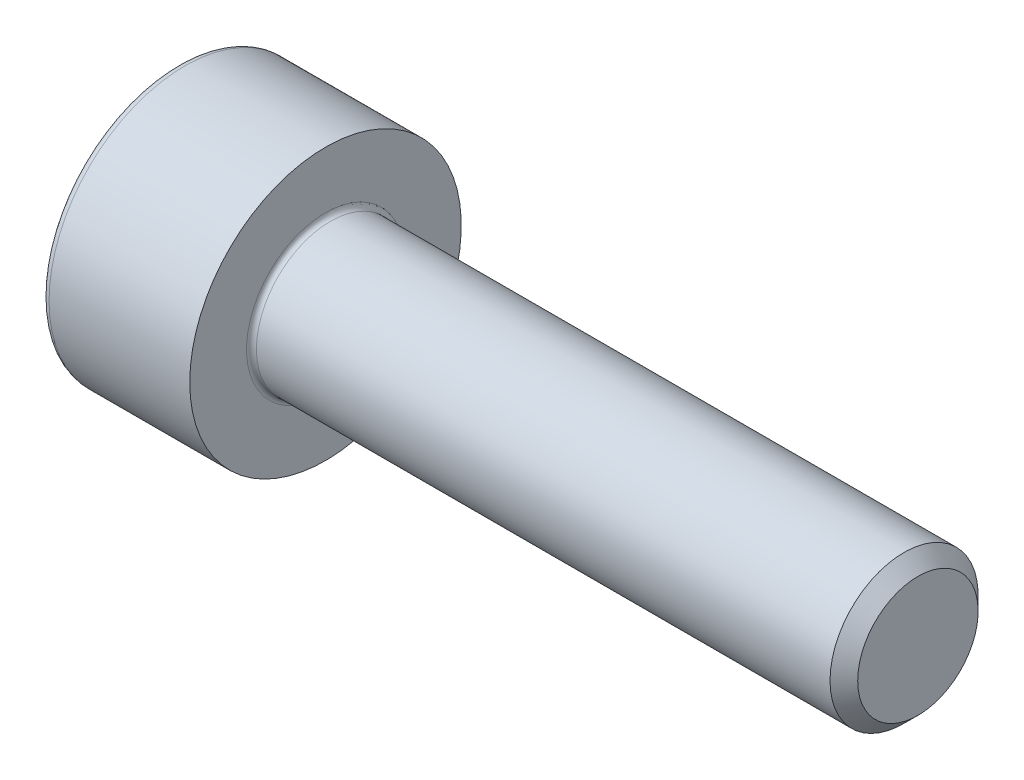
SolidWorks part; units mm, degrees
revolve "Base-Revolve" add sketch "BodySke"
sketch "BodySke" plane through (0, 0, 0) normal (0, 0, 1) x (1, 0, 0)
  line L0 (0, 0) -> (0, 2.75)
  line L1 (0, 2.75) -> (3, 2.75)
  line L2 (3, 2.75) -> (3, 1.5)
  line L3 (3, 1.5) -> (14.7195, 1.5)
  line L4 (15, 1.2195) -> (15, 0)
  line L5 (15, 0) -> (0, 0)
  line L6 (-31.75, 0) -> (127, 0) construction
  line L8 (15, 1.2195) -> (14.7195, 1.5)
  line L10 (15, -1.2195) -> (14.7195, -1.5) construction
  line L11 (3.5, 9.525) -> (3.5, 3.175) construction
  line L12 (3, 9.525) -> (3, 3.175) construction
  line L13 (-45, 9.525) -> (-45, 3.175) construction
  dimension "Head_ht" = 3
  dimension "Length" = 12
  dimension "Body_ch_ang" = 45
  dimension "Diameter" = 3
  dimension "Minor_dia" = 2.439
  dimension "Advance" = 0.5
  dimension "Thread_nom" = 12
  dimension "Thread_length" = 60
  dimension "Head_dia" = 5.5
cosmetic thread "ThreadCosmetic" [suppressed]
fillet "Fillet1" radius 0.1 1 edges at (3, 0, 1.5)
fillet "Fillet2" radius 0.15 1 edges at (0, 0, 2.75)
ref_plane "Plane1" through (0, 0, 0) normal (0, 0, 1) x (1, 0, 0)
ref_plane "Plane2" through (0, 0, 0) normal (0, 1, 0) x (1, 0, 0)
ref_plane "Plane3" through (0, 0, 0) normal (1, 0, 0) x (0, 0, -1)
sketch "Sketch2" plane through (0, 0, 0) normal (0, 0, 1) x (1, 0, 0)
  line L0 (0, 1.28) -> (1.3, 1.28)
  line L1 (1.3, 1.28) -> (2.039, 0)
  line L2 (-31.75, 0) -> (127, 0) construction
  line L3 (2.039, 0) -> (0, 0)
  line L4 (0, 0) -> (0, 1.28)
  line L6 (0, 0) -> (47.625, 0) construction
  dimension "D1" = 1.28
  dimension "D2" = 60
  dimension "Depth" = 1.3
revolve "Hex-PreBroach" cut sketch "Sketch2" angle 360 about L6
sketch "Sketch3" plane through (0, 0, 0) normal (-1, 0, 0) x (0, 0.5, 0.866)
  line L0 (0.739, 1.28) -> (-0.739, 1.28)
  line L1 (-0.739, 1.28) -> (-1.478, 0)
  line L2 (0.739, 1.28) -> (1.478, 0)
  line L3 (0.739, -1.28) -> (1.478, 0)
  line L4 (0.739, -1.28) -> (-0.739, -1.28)
  line L5 (-0.739, -1.28) -> (-1.478, 0)
  dimension "D1" = 1.28
  dimension "D2" = 1.28
  dimension "Hex_size" = 2.56
extrude "Hex" cut sketch "Sketch3" against normal blind 1.3
sketch "ThdSchSke" plane through (0, 0, 0) normal (0, 0, 1) x (1, 0, 0)
  line L0 (4.5, -1.2195) -> (4.3036, -1.5)
  line L1 (4.5, -1.2195) -> (4.6964, -1.5)
  line L2 (4.6964, -1.5) -> (4.6964, -1.875)
  line L3 (-3.175, 0) -> (5.1513, 0) construction
  line L4 (0, 2.6) -> (0, -2.6) construction
  line L5 (4.6964, -1.875) -> (4.3036, -1.875)
  line L6 (4.3036, -1.875) -> (4.3036, -1.5)
  dimension "Thread_minor" = 2.439
  dimension "Diameter" = 3
  dimension "Start" = 4.5
revolve "ThreadSchematic" [suppressed] cut sketch "ThdSchSke" angle 360 about L3
pattern_linear "ThdSchPat" [suppressed]
equation "\"D2@Sketch3\" = \"Hex_size@Sketch3\" / 2"
equation "\"D1@Sketch3\" = \"Hex_size@Sketch3\" / 2"
equation "\"D1@Sketch2\" = \"Hex_size@Sketch3\" / 2"
equation "\"Thread_minor@ThreadCosmetic\"  =  \"Minor_dia@BodySke\""
equation "\"Depth@Sketch2\" =  \"Key_eng@Hex\""
equation "\"Thread_length@ThreadCosmetic\" = ((sgn( (\"Length@BodySke\" - \"Advance@BodySke\" * 3.0) - \"Thread_nom@BodySke\" )-1)*( (\"Length@BodySke\" - \"Advance@BodySke\" * 3.0) - \"Thread_nom@BodySke\" ))/-2+ \"Thread_nom@BodySke\""
equation "\"Thread_minor@ThdSchSke\" = \"Minor_dia@BodySke\""
equation "\"Diameter@ThdSchSke\" = \"Diameter@BodySke\""
equation "\"Overcut@ThdSchSke\" = \"Diameter@BodySke\" * 1.25"
equation "\"Start@ThdSchSke\" = \"Head_ht@BodySke\" + \"Length@BodySke\" - \"Thread_length@ThreadCosmetic\"  '---Non-countersunk---"
equation "\"Num_threads@ThdSchPat\" = int( \"Thread_length@ThreadCosmetic\" / \"Advance@BodySke\" + 0.999 )  + 1"
equation "\"Advance@ThdSchPat\" = \"Thread_length@ThreadCosmetic\" /  (\"Num_threads@ThdSchPat\" - 1) 'relax it"
equation "\"Num_threads@ThdSchPat\" = \"Num_threads@ThdSchPat\" - sgn( \"Num_threads@ThdSchPat\" - 1) '---chamfered tips only---"
